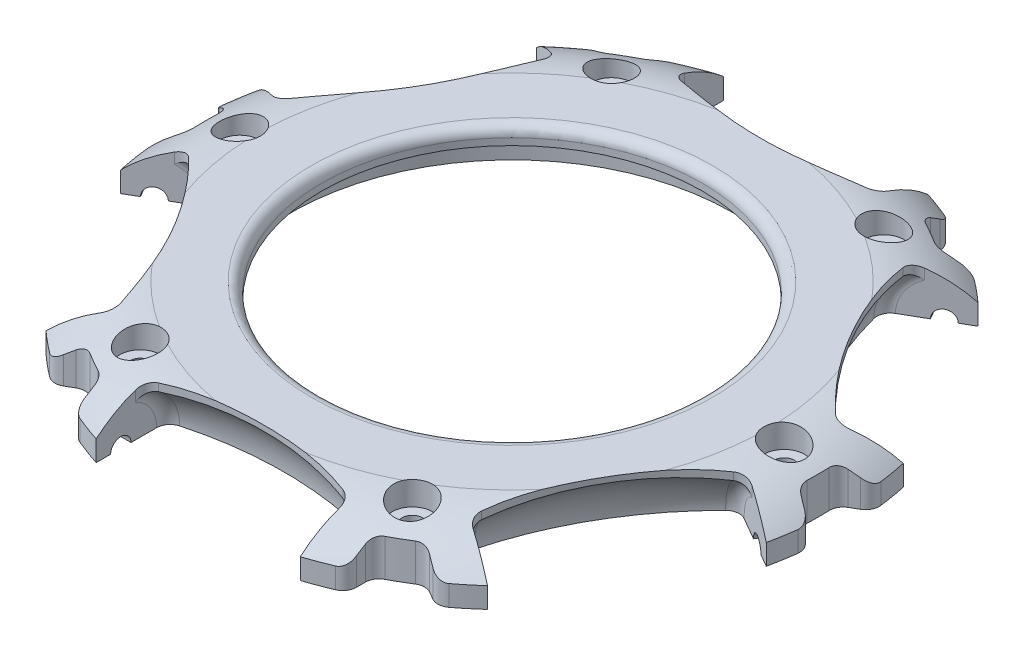
SolidWorks part; units mm, degrees
ref_plane "Front Plane" through (0, 0, 0) normal (0, 0, 1) x (1, 0, 0)
ref_plane "Top Plane" through (0, 0, 0) normal (0, 1, 0) x (1, 0, 0)
ref_plane "Right Plane" through (0, 0, 0) normal (1, 0, 0) x (0, 0, -1)
sketch "Sketch1" plane through (0, 0, 0) normal (0, 1, 0) x (1, 0, 0)
  line L10 (0, 0) -> (0, -50) construction
  line L11 (15, -42.5) -> (-15, -42.5) construction
  line L12 (15, -37.303) -> (15, -47.697)
  line L13 (-15, -37.303) -> (-15, -47.697)
  line L14 (-24.8054, -31.6419) -> (-33.8068, -36.8389)
  line L15 (-39.8054, -5.6611) -> (-48.8068, -10.8581)
  line L16 (-29.3061, -34.2404) -> (-44.3061, -8.2596) construction
  line L17 (-39.8054, 5.6611) -> (-48.8068, 10.8581)
  line L18 (-24.8054, 31.6419) -> (-33.8068, 36.8389)
  line L19 (-44.3061, 8.2596) -> (-29.3061, 34.2404) construction
  line L20 (-15, 37.303) -> (-15, 47.697)
  line L21 (15, 37.303) -> (15, 47.697)
  line L22 (-15, 42.5) -> (15, 42.5) construction
  line L23 (24.8054, 31.6419) -> (33.8068, 36.8389)
  line L24 (39.8054, 5.6611) -> (48.8068, 10.8581)
  line L25 (29.3061, 34.2404) -> (44.3061, 8.2596) construction
  line L26 (39.8054, -5.6611) -> (48.8068, -10.8581)
  line L27 (24.8054, -31.6419) -> (33.8068, -36.8389)
  line L28 (44.3061, -8.2596) -> (29.3061, -34.2404) construction
  line L103 (-16.5, -36.2148) -> (-16.5, -47.697)
  line L104 (16.5, -36.2148) -> (16.5, -47.697)
  circle A3 centre (0, 0) radius 50
  circle A4 centre (0, 0) radius 42.5 construction
  arc A8 (-15, -37.303) -> (15, -37.303) centre (0, -85) cw
  arc A9 (-39.8054, -5.6611) -> (-24.8054, -31.6419) centre (-73.6122, -42.5) cw
  arc A10 (-24.8054, 31.6419) -> (-39.8054, 5.6611) centre (-73.6122, 42.5) cw
  arc A11 (15, 37.303) -> (-15, 37.303) centre (0, 85) cw
  arc A12 (39.8054, 5.6611) -> (24.8054, 31.6419) centre (73.6122, 42.5) cw
  arc A13 (24.8054, -31.6419) -> (39.8054, -5.6611) centre (73.6122, -42.5) cw
  circle A38 centre (0, 0) radius 33.5
  circle A39 centre (0, 0) radius 28
  arc A40 (-16.5, -36.2148) -> (16.5, -36.2148) centre (0, -85) cw
  circle A41 centre (0, 0) radius 31
  point P18 (0, -42.5)
  point P28 (-36.8061, -21.25)
  point P36 (-36.8061, 21.25)
  point P44 (0, 42.5)
  point P52 (36.8061, 21.25)
  point P60 (36.8061, -21.25)
  point P65 (0, 0)
  dimension "D1" = 30
  dimension "D2" = 100
  dimension "D3" = 85
  dimension "D4" = 6
  dimension "D5" = 1.5
  dimension "D6" = 2.5
  dimension "D7" = 3
sketch "Sketch2" plane through (0, 0, 0) normal (0, 1, 0) x (1, 0, 0)
  circle A0 centre (0, 0) radius 50 construction
  circle A1 centre (0, 0) radius 50
extrude "Boss-Extrude1" add sketch "Sketch2" along normal blind 7.5
sketch "Sketch3" plane through (0, 0, 0) normal (0, 1, 0) x (1, 0, 0)
  line L5 (-20.18, -42.5) -> (20.5663, -42.5) construction
  line L6 (-15, -42.5) -> (15, -42.5)
  line L7 (-15, -42.5) -> (-15, -35.7329)
  line L8 (15, -42.5) -> (15, -35.7329)
  arc A0 (16.5, -36.2148) -> (-16.5, -36.2148) centre (0, -85) ccw construction
  arc A1 (15, -35.7329) -> (-15, -35.7329) centre (0, -85) ccw
revolve "Cut-Revolve1" cut sketch "Sketch3" angle 360 about L5
sketch "Sketch4" plane through (0, 0, 0) normal (0, 1, 0) x (1, 0, 0)
  line L5 (15, -38.8779) -> (15, -47.697)
  line L6 (-15, -37.303) -> (-15, -47.697) construction
  line L7 (-15, -38.8779) -> (-15, -47.697)
  arc A0 (16.5, -36.2148) -> (-16.5, -36.2148) centre (0, -85) ccw construction
  arc A1 (16.5, -36.2148) -> (-16.5, -36.2148) centre (0, -85) ccw construction
  arc A2 (15, -38.8779) -> (-15, -38.8779) centre (0, -85) ccw
  circle A3 centre (0, 0) radius 50 construction
  arc A4 (-15, -47.697) -> (15, -47.697) centre (0, 0) ccw
  dimension "D1" = 3
extrude "Cut-Extrude2" cut sketch "Sketch4" along normal up to next (7.5 mm away)
sketch "Sketch5" plane through (0, 0, 0) normal (1, 0, 0) x (0, 0, -1)
  circle A0 centre (-42.5, 0) radius 1.5
  point P0 (-42.5, 0)
  dimension "D1" = 3
extrude "Cut-Extrude3" cut sketch "Sketch5" against normal blind 18 and the other way blind 18
pattern_circular "CirPattern1" count 6 over 360 about axis through (0, 0, 0) along (0, 1, 0) of "Cut-Revolve1", "Cut-Extrude2", "Cut-Extrude3"
sketch "Sketch6" plane through (0, 0, 0) normal (0, -1, 0) x (1, 0, 0)
  line L0 (-29.1051, 37.5885) -> (-26.507, 36.0885) construction
  line L1 (-18, 44) -> (-18, 41) construction
  line L2 (-29.1051, 37.5885) -> (-26.507, 36.0885) construction
  line L3 (-18, 44) -> (-18, 41) construction
  line L4 (-20, 44) -> (-20, 41) construction
  line L5 (-28.1051, 39.3205) -> (-25.507, 37.8205) construction
  line L6 (-28.2647, 39.4126) -> (-24.9106, 37.4762)
  line L7 (-20, 40.3113) -> (-20, 44.1843)
  line L8 (20, 44.1843) -> (20, 40.3113)
  line L9 (24.9106, 37.4762) -> (28.2647, 39.4126)
  line L10 (48.2647, 4.7716) -> (44.9106, 2.8351)
  line L11 (44.9106, -2.8351) -> (48.2647, -4.7716)
  line L12 (28.2647, -39.4126) -> (24.9106, -37.4762)
  line L13 (20, -40.3113) -> (20, -44.1843)
  line L14 (-20, -44.1843) -> (-20, -40.3113)
  line L15 (-24.9106, -37.4762) -> (-28.2647, -39.4126)
  line L16 (-48.2647, -4.7716) -> (-44.9106, -2.8351)
  line L17 (-44.9106, 2.8351) -> (-48.2647, 4.7716)
  circle A1 centre (0, 0) radius 50 construction
  arc A4 (-20, 40.3113) -> (-24.9106, 37.4762) centre (0, 0) ccw
  arc A5 (-28.2647, 39.4126) -> (-48.2647, 4.7716) centre (0, 0) ccw
  arc A6 (24.9106, 37.4762) -> (20, 40.3113) centre (0, 0) ccw
  circle A7 centre (0, 0) radius 50
  arc A10 (44.9106, -2.8351) -> (44.9106, 2.8351) centre (0, 0) ccw
  arc A12 (20, -40.3113) -> (24.9106, -37.4762) centre (0, 0) ccw
  arc A14 (-24.9106, -37.4762) -> (-20, -40.3113) centre (0, 0) ccw
  arc A16 (-44.9106, 2.8351) -> (-44.9106, -2.8351) centre (0, 0) ccw
  arc A18 (20, 44.1843) -> (-20, 44.1843) centre (0, 0) ccw
  arc A19 (48.2647, 4.7716) -> (28.2647, 39.4126) centre (0, 0) ccw
  arc A20 (28.2647, -39.4126) -> (48.2647, -4.7716) centre (0, 0) ccw
  arc A21 (-20, -44.1843) -> (20, -44.1843) centre (0, 0) ccw
  arc A22 (-48.2647, -4.7716) -> (-28.2647, -39.4126) centre (0, 0) ccw
  point P1 (48.5, 0)
  point P15 (43.0337, 13.1567)
  point P48 (0, 0)
  dimension "D5" = 6
  dimension "D3" = 2
  dimension "D4" = 2
extrude "Cut-Extrude4" cut sketch "Sketch6" against normal up to next
sketch "Sketch8" plane through (0, 0, 0) normal (0, -1, 0) x (1, 0, 0)
  circle A2 centre (0, 0) radius 32.5
  circle A3 centre (0, 0) radius 32.5
  dimension "D1" = 1
extrude "Cut-Extrude5" cut sketch "Sketch8" against normal offset from surface (5 mm away) 2.5 up to face at (0, 7.5, 0)
sketch "Sketch9" plane through (0, 0, 0) normal (0, -1, 0) x (1, 0, 0)
  line L0 (0, 0) -> (32.5, 0) construction
  line L1 (32.5, 0) -> (40, 0) construction
  circle A0 centre (0, 0) radius 32.5 construction
  circle A1 centre (40, 0) radius 1.5
  dimension "D2" = 3
  dimension "D1" = 40
extrude "Cut-Extrude6" cut sketch "Sketch9" against normal up to next (7.5 mm away)
sketch "Sketch10" plane through (0, 7.5, 0) normal (0, 1, 0) x (1, 0, 0)
  circle A0 centre (40, 0) radius 3
extrude "Cut-Extrude7" cut sketch "Sketch10" against normal offset from surface (3.5 mm away) 4 up to face at (40, 0, -1.5)
pattern_circular "CirPattern2" count 6 over 360 about axis through (0, 0, 0) along (0, 1, 0) of "Cut-Extrude7", "Cut-Extrude6"
sketch "Sketch7" plane through (0, 0, 0) normal (0, 0, 1) x (1, 0, 0)
  line L0 (-50, 0) -> (-50, 1.5) construction
  line L1 (50, 0) -> (-50, 0) construction
  line L2 (-26.1692, 7.5) -> (-41.1692, 7.5) construction
  line L3 (-37.542, 7.5) -> (-50, 7.5)
  line L4 (-50, 7.5) -> (-50, 1.5)
  line L5 (0, 0) -> (0, 7.5) construction
  line L6 (15, 7.5) -> (-15, 7.5) construction
  spline S0 degree 2 poles (-50, 1.5) (-45.2094, 6.974) (-37.542, 7.5) knots 0 0 0 1 1 1
revolve "Cut-Revolve2" cut sketch "Sketch7" angle 360 about L5
fillet "Fillet1" radius 2 12 edges at (-44.9106, 2.7403, -2.8351) (-44.9106, 2.7403, 2.8351) (-20, 2.7403, -40.3113) (-24.9106, 2.7403, -37.4762) (24.9106, 2.7403, -37.4762) (20, 2.7403, -40.3113) (44.9106, 2.7403, 2.8351) (44.9106, 2.7403, -2.8351) (24.9106, 2.7403, 37.4762) (20, 2.7403, 40.3113) (-20, 2.7403, 40.3113) (-24.9106, 2.7403, 37.4762)
sketch "Sketch11" plane through (0, 5, 0) normal (0, -1, 0) x (1, 0, 0)
  circle A0 centre (0, 0) radius 5
fillet "Fillet2" radius 2 24 edges at (24.1714, 3.2621, -31.2759) (26.1692, 6.2583, -32.4293) (39.1714, 3.2621, -5.2951) (41.1692, 6.2583, -6.4486) (39.1714, 3.2621, 5.2951) (41.1692, 6.2583, 6.4486) (24.1714, 3.2621, 31.2759) (26.1692, 6.2583, 32.4293) (15, 6.2583, 38.8779) (15, 3.2621, 36.571) (-15, 3.2621, 36.571) (-15, 6.2583, 38.8779) (-26.1692, 6.2583, 32.4293) (-24.1714, 3.2621, 31.2759) (-41.1692, 6.2583, 6.4486) (-39.1714, 3.2621, 5.2951) (-41.1692, 6.2583, -6.4486) (-39.1714, 3.2621, -5.2951) (-26.1692, 6.2583, -32.4293) (-24.1714, 3.2621, -31.2759) (-15, 6.2583, -38.8779) (-15, 3.2621, -36.571) (15, 3.2621, -36.571) (15, 6.2583, -38.8779)
fillet "Fillet3" radius 2 12 edges at (-48.2647, 1.5146, 4.7716) (-48.2647, 1.5146, -4.7716) (-28.2647, 1.5146, -39.4126) (-20, 1.5146, -44.1843) (20, 1.5146, -44.1843) (28.2647, 1.5146, -39.4126) (48.2647, 1.5146, -4.7716) (48.2647, 1.5146, 4.7716) (20, 1.5146, 44.1843) (28.2647, 1.5146, 39.4126) (-28.2647, 1.5146, 39.4126) (-20, 1.5146, 44.1843)
sketch "Sketch12" plane through (0, 5, 0) normal (0, -1, 0) x (1, 0, 0)
  circle A0 centre (0, 0) radius 28
  dimension "D1" = 56
extrude "Cut-Extrude8" cut sketch "Sketch12" against normal up to next
fillet "Fillet4" radius 1.5 1 edges at (0, 7.5, 28)
